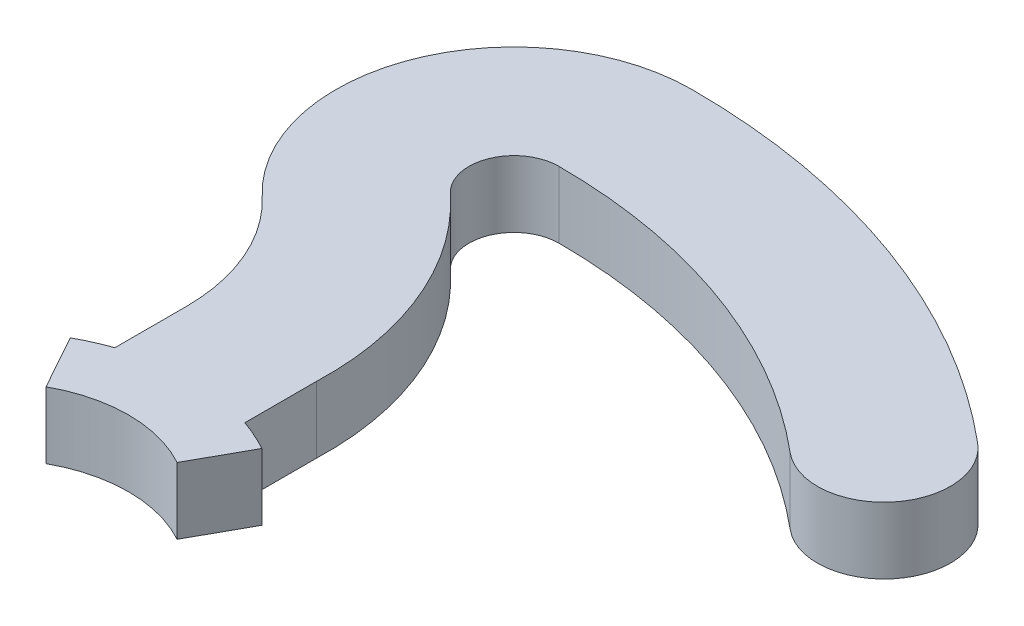
SolidWorks part; units mm, degrees
ref_plane "Front Plane" through (0, 0, 0) normal (0, 0, 1) x (1, 0, 0)
ref_plane "Top Plane" through (0, 0, 0) normal (0, 1, 0) x (1, 0, 0)
ref_plane "Right Plane" through (0, 0, 0) normal (1, 0, 0) x (0, 0, -1)
sketch "Sketch6" plane through (0, 0, 0) normal (1, 0, 0) x (0, 0, -1)
  line L0 (0, 0) -> (0, 22.6667) construction
sketch "Sketch8" plane through (0, 0, 0) normal (0, 1, 0) x (1, 0, 0)
  line L0 (-6.254, 11.2826) -> (-9.1387, 16.4866)
  line L2 (-6.2, 17.8012) -> (-6.2, 24.6317)
  line L3 (6.254, 11.2826) -> (9.1387, 16.4866)
  line L5 (6.2, 17.8012) -> (6.2, 24.6317)
  line L6 (0, 0) -> (0, -31.8547) construction
  line L7 (0.1876, -0.5154) -> (-19.8533, 54.5466) construction
  line L8 (0, 0) -> (20.0409, 55.062) construction
  line L9 (-0.4818, -0.5742) -> (3.3161, 3.952) construction
  line L10 (3.8023, 37.1033) -> (3.8023, 37.1033)
  line L11 (3.8023, 37.1033) -> (3.8023, 37.1033)
  line L12 (3.8023, 37.1033) -> (3.8023, 37.1033)
  line L13 (3.8023, 37.1033) -> (3.8023, 37.1033)
  line L14 (3.8023, 37.1033) -> (3.8023, 37.1033)
  line L15 (3.8023, 37.1033) -> (3.8023, 37.1033)
  line L16 (-9.1387, 16.4866) -> (-6.2, 17.8012) construction
  line L17 (9.1387, 16.4866) -> (6.2, 17.8012) construction
  arc A0 (6.254, 11.2826) -> (-6.254, 11.2826) centre (0, 0) ccw
  arc A2 (0, 66.675) -> (-11.6721, 37.3333) centre (0, 49.6826) ccw
  arc A3 (-6.2, 24.6317) -> (-11.6721, 37.3333) centre (-23.6772, 24.6317) ccw
  arc A4 (-9.1387, 16.4866) -> (-6.2, 17.8012) centre (0, 0) cw
  arc A5 (-6.2, 24.6317) -> (6.2, 24.6317) centre (0, 0) cw construction
  arc A6 (34.6945, 41.3472) -> (42.8579, 51.076) centre (38.7762, 46.2116) ccw
  arc A7 (42.8579, 51.076) -> (0, 66.675) centre (0, 0) ccw
  arc A8 (34.6945, 41.3472) -> (0, 53.975) centre (0, 0) ccw
  arc A9 (0, 53.975) -> (-2.9485, 46.563) centre (0, 49.6826) ccw
  arc A10 (6.2, 17.8012) -> (9.1387, 16.4866) centre (0, 0) cw
  arc A11 (3.8023, 37.1033) -> (3.8023, 37.1033) centre (3.8023, 37.1033) cw
  arc A12 (6.2, 24.6317) -> (-2.9485, 46.563) centre (-22.2919, 25.6203) ccw
  arc A13 (3.8023, 37.1033) -> (-2.9485, 46.563) centre (-23.6772, 24.6317) ccw construction
  point P41 (0, 0)
  point P44 (3.7147, 37.017)
  dimension "D4" = 12.9
  dimension "D8" = 18.85
  dimension "D10" = 25.4
  dimension "D12" = 66.675
  dimension "D2" = 20
  dimension "D3" = 20
  dimension "D5" = 58
  dimension "D6" = 29
  dimension "D7" = 12.4
  dimension "D9" = 6.2
  dimension "D13" = 12.7
extrude "Boss-Extrude1" add sketch "Sketch8" along normal mid plane 6.35
sketch "Sketch12" plane through (0, 0, 0) normal (0, 1, 0) x (1, 0, 0)
  line L0 (0, 0) -> (0, 72.7351) construction
  line L1 (0, 0) -> (-10.2676, 22.6939) construction
  line L2 (0, 0) -> (10.2676, 22.6939) construction
  point P5 (-7.7767, 17.1883)
  point P6 (-10.2676, 22.6939)
  point P8 (0, 0)
  dimension "D1" = 24.344
hole_wizard "Ø1.0mm Dowel Hole1" positions "3DSketch1" profile "Sketch15" hole size "Ø1.0" standard "ANSI Metric"
sketch3d "3DSketch1"
  line L0 (0, 0, 0) -> (10.2676, 0, -22.6939) construction
  point P0 (7.7702, 0, -17.174)
sketch "Sketch15" plane through (7.7702, 0, -17.174) normal (0, 1, 0) x (-0.9111, 0, -0.4122)
  line L0 (0, 0) -> (0, 5.95)
  line L1 (0, 5.95) -> (1.0581, 5.95)
  line L2 (1.0581, 5.95) -> (1.0581, 0)
  line L5 (1.0581, 0) -> (0, 0)
  line L11 (0, -6.35) -> (0, 107.95) construction
  dimension "Thru Hole Dia." = 2.1162
  dimension "Thru Hole Depth" = 5.95
hole_wizard "Ø1.0mm Dowel Hole2" positions "3DSketch2" profile "Sketch16" hole size "Ø1.0" standard "ANSI Metric"
sketch3d "3DSketch2"
  line L0 (0, 0, 0) -> (-10.2676, 0, -22.6939) construction
  point P0 (-7.7702, 0, -17.174)
sketch "Sketch16" plane through (-7.7702, 0, -17.174) normal (0, 1, 0) x (-0.9111, 0, 0.4122)
  line L0 (0, 0) -> (0, 5.95)
  line L1 (0, 5.95) -> (1.0581, 5.95)
  line L2 (1.0581, 5.95) -> (1.0581, 0)
  line L5 (1.0581, 0) -> (0, 0)
  line L11 (0, -6.35) -> (0, 107.95) construction
  dimension "Thru Hole Dia." = 2.1162
  dimension "Thru Hole Depth" = 5.95
